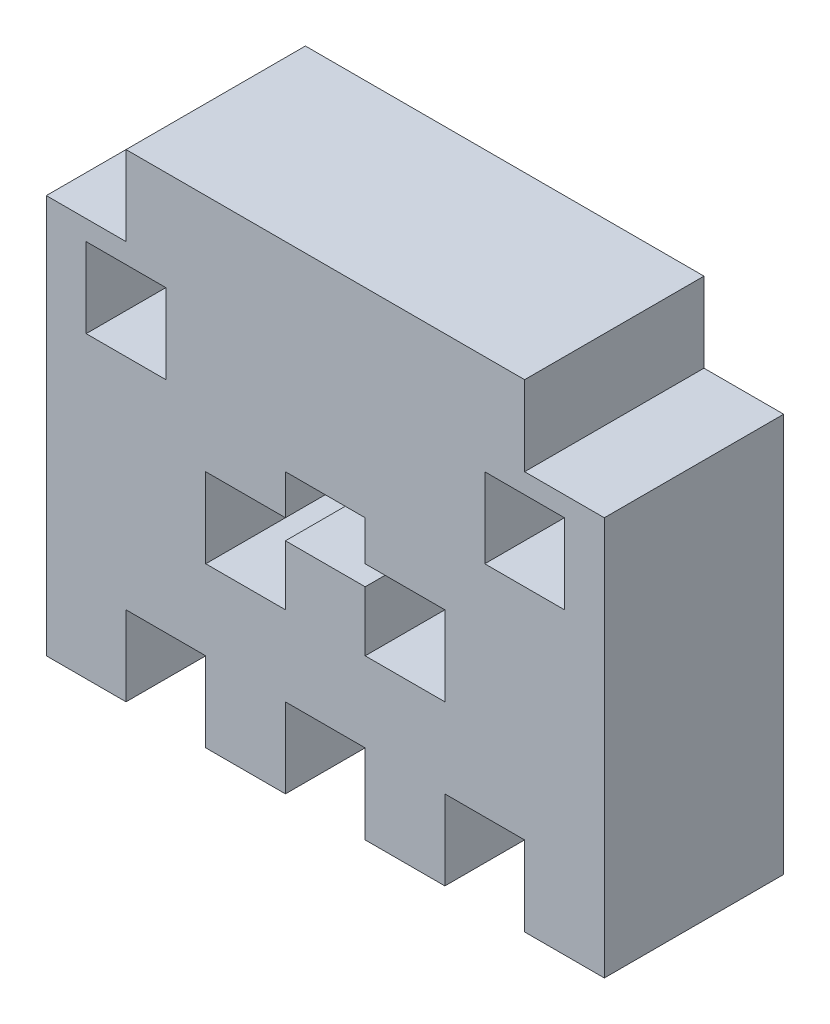
SolidWorks part; units mm, degrees
ref_plane "Front" through (0, 0, 0) normal (0, 0, 1) x (1, 0, 0)
ref_plane "Top" through (0, 0, 0) normal (0, 1, 0) x (1, 0, 0)
ref_plane "Right" through (0, 0, 0) normal (1, 0, 0) x (0, 0, -1)
sketch "Sketch1" plane through (0, 0, 0) normal (0, 0, 1) x (1, 0, 0)
  line L0 (20, 0) -> (20, 20)
  line L1 (0, 0) -> (20, 0)
  line L2 (0, 0) -> (0, 100)
  line L3 (20, 120) -> (120, 120)
  line L4 (140, 0) -> (140, 100)
  line L5 (40, 0) -> (40, 20)
  line L6 (60, 0) -> (60, 20)
  line L7 (80, 0) -> (80, 20)
  line L8 (100, 0) -> (100, 20)
  line L9 (120, 0) -> (120, 20)
  line L10 (20, 20) -> (40, 20)
  line L11 (0, 100) -> (20, 100)
  line L12 (40, 0) -> (60, 0)
  line L13 (0, 0) -> (140, 0) construction
  line L14 (80, 0) -> (100, 0)
  line L15 (120, 0) -> (140, 0)
  line L16 (0, 20) -> (140, 20) construction
  line L17 (100, 20) -> (120, 20)
  line L18 (60, 20) -> (80, 20)
  line L20 (0, 120) -> (140, 120) construction
  line L21 (0, 0) -> (0, 120) construction
  line L22 (40, 0) -> (40, 120) construction
  line L23 (60, 0) -> (60, 120) construction
  line L24 (80, 0) -> (80, 120) construction
  line L25 (100, 0) -> (100, 120) construction
  line L26 (120, 100) -> (140, 100)
  line L27 (0, 100) -> (140, 100) construction
  line L28 (20, 100) -> (20, 120)
  line L29 (20, 0) -> (20, 120) construction
  line L30 (120, 100) -> (120, 120)
  line L31 (120, 0) -> (120, 120) construction
  line L32 (10, 95) -> (30, 95)
  line L33 (110, 95) -> (130, 95)
  line L34 (40, 40) -> (60, 40)
  line L35 (60, 40) -> (80, 40) construction
  line L36 (60, 55) -> (80, 55)
  line L37 (40, 60) -> (60, 60)
  line L38 (60, 70) -> (80, 70)
  line L39 (80, 60) -> (100, 60)
  line L40 (40, 60) -> (100, 60) construction
  line L41 (60, 60) -> (60, 70)
  line L42 (80, 60) -> (80, 70)
  line L43 (40, 55) -> (100, 55) construction
  line L44 (40, 40) -> (40, 60)
  line L45 (60, 40) -> (60, 55)
  line L46 (80, 40) -> (100, 40)
  line L47 (40, 40) -> (100, 40) construction
  line L48 (80, 40) -> (80, 55)
  line L49 (100, 40) -> (100, 60)
  line L50 (110, 75) -> (130, 75)
  line L51 (10, 75) -> (30, 75)
  line L53 (10, 95) -> (10, 75)
  line L55 (110, 95) -> (110, 75)
  line L56 (30, 95) -> (30, 75)
  line L57 (130, 95) -> (130, 75)
  line L58 (120, 95) -> (140, 95) construction
  line L59 (120, 75) -> (140, 75) construction
  line L60 (0, 95) -> (20, 95) construction
  line L61 (0, 75) -> (20, 75) construction
extrude "Extrude1" add sketch "Sketch1" along normal blind 45
